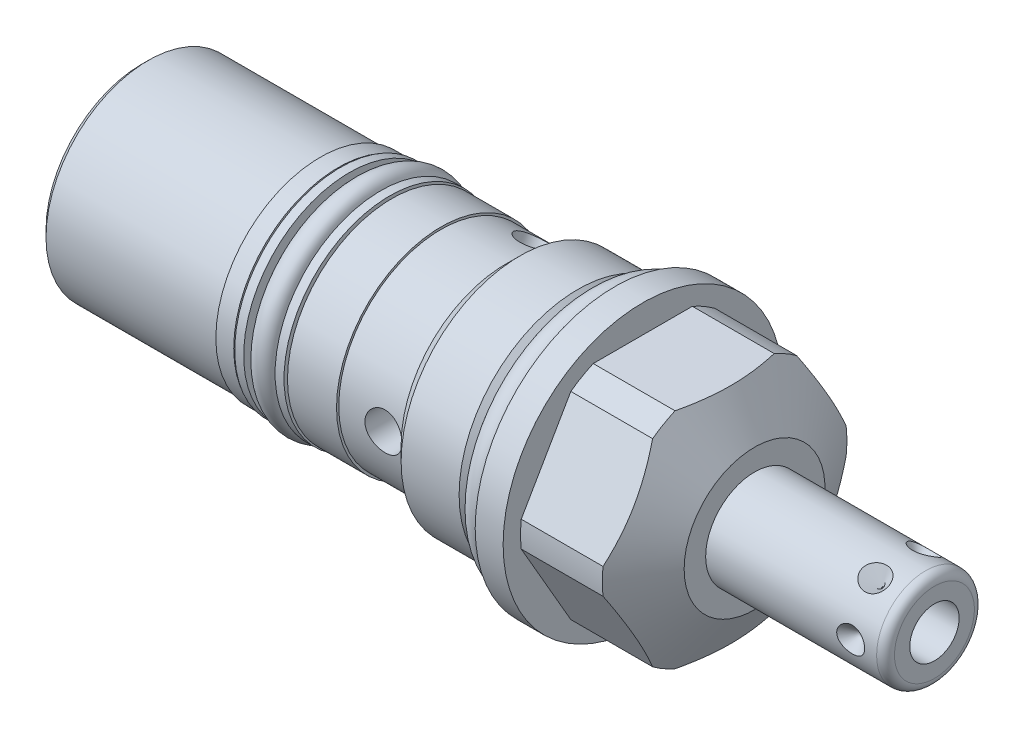
SolidWorks part; units mm, degrees
material "Alloy Steel"
ref_plane "Front Plane" through (0, 0, 0) normal (0, 0, 1) x (1, 0, 0)
ref_plane "Top Plane" through (0, 0, 0) normal (0, 1, 0) x (1, 0, 0)
ref_plane "Right Plane" through (0, 0, 0) normal (1, 0, 0) x (0, 0, -1)
sketch "Sketch1" plane through (0, 0, 0) normal (0, 0, 1) x (1, 0, 0)
  line L0 (0, 0) -> (113.8544, 0) construction
  line L1 (0, 15.875) -> (3.175, 15.875)
  line L2 (3.175, 15.875) -> (3.175, 13.8938)
  line L3 (3.175, 13.8938) -> (12.4728, 13.8938)
  line L4 (12.4728, 13.8938) -> (15.875, 8.001)
  line L5 (15.875, 8.001) -> (15.875, 0)
  line L6 (15.875, 0) -> (-53.7972, 0)
  line L7 (-53.7972, 0) -> (-53.7972, 11.6205)
  line L8 (0, 15.875) -> (0, 12.0015)
  line L9 (0, 12.0015) -> (-2.7178, 12.0015)
  line L10 (-2.7178, 12.0015) -> (-4.21, 13.4937)
  line L11 (-4.21, 13.4937) -> (-10.8013, 13.4937)
  line L12 (-10.8013, 13.4937) -> (-12.4206, 11.8745)
  line L14 (-12.4206, 11.8745) -> (-12.4206, 11.6205)
  line L15 (-12.4206, 11.6205) -> (-53.7972, 11.6205)
  dimension "D1" = 31.75
  dimension "D2" = 16.002
  dimension "D3" = 3.175
  dimension "D4" = 15.875
  dimension "D5" = 27.7876
  dimension "D6" = 30
  dimension "D7" = 53.7972
  dimension "D8" = 51.0794
  dimension "D9" = 24.003
  dimension "D10" = 45
  dimension "D11" = 26.9875
  dimension "D12" = 9.7028
  dimension "D13" = 23.749
  dimension "D14" = 23.241
revolve "Revolve1" add sketch "Sketch1" angle 360 about L0
sketch "Sketch2" plane through (15.875, 0, 0) normal (1, 0, 0) x (0, 0, -1)
  line L1 (7.3323, 12.7) -> (-7.3323, 12.7)
  line L2 (-7.3323, 12.7) -> (-14.6647, 0)
  line L3 (-14.6647, 0) -> (-7.3323, -12.7)
  line L4 (-7.3323, -12.7) -> (7.3323, -12.7)
  line L5 (7.3323, -12.7) -> (14.6647, 0)
  line L6 (14.6647, 0) -> (7.3323, 12.7)
  circle A0 centre (0, 0) radius 12.7 construction
  dimension "D1" = 25.4
extrude "Cut-Extrude1" cut sketch "Sketch2" against normal up to surface (12.7 mm away) flip side to cut up to face at (3.175, 0, 15.875)
sketch "Sketch3" plane through (0, 0, 0) normal (0, 0, 1) x (1, 0, 0)
  line L0 (0, 0) -> (52.5154, 0) construction
  line L1 (15.875, 5.5563) -> (35.306, 5.5562)
  line L2 (15.875, -8.001) -> (15.875, 8.001) construction
  line L3 (36.322, 4.5402) -> (36.322, 0)
  line L4 (36.322, 0) -> (15.875, 0)
  line L5 (15.875, 0) -> (15.875, 5.5563)
  line L6 (0, 15.875) -> (0, -15.875) construction
  arc A0 (36.322, 4.5402) -> (35.306, 5.5562) centre (35.306, 4.5402) ccw
  dimension "D1" = 1.016
  dimension "D2" = 36.322
  dimension "D3" = 11.1125
revolve "Revolve2" add sketch "Sketch3" angle 360 about L0
sketch "Sketch4" plane through (0, 0, 0) normal (0, 1, 0) x (1, 0, 0)
  line L0 (32.3596, 10.0738) -> (32.3596, 0) construction
  line L1 (36.322, -4.5402) -> (36.322, 4.5402) construction
  line L2 (33.9471, 5.5563) -> (32.3596, 5.5563)
  line L3 (35.306, 5.5563) -> (15.875, 5.5563) construction
  line L4 (32.3596, 5.5563) -> (32.3596, 3.9687)
  line L5 (32.3596, 3.9687) -> (33.9471, 5.5563)
  dimension "D1" = 3.9624
  dimension "D2" = 45
  dimension "D3" = 3.175
revolve "Cut-Revolve1" cut sketch "Sketch4" angle 360 about L0
pattern_circular "CirPattern1" count 6 over 360 about axis through (0, 0, 0) along (-1, 0, 0) of "Cut-Revolve1"
sketch "Sketch5" plane through (0, 0, 0) normal (0, 0, 1) x (1, 0, 0)
  line L0 (0, 0) -> (44.9273, 0) construction
  line L1 (36.322, 2.8067) -> (26.162, 2.8067)
  line L2 (36.322, -4.5402) -> (36.322, 4.5402) construction
  line L3 (26.162, 2.8067) -> (24.4756, 0)
  line L4 (24.4756, 0) -> (36.322, 0)
  line L5 (36.322, 0) -> (36.322, 2.8067)
  dimension "D1" = 10.16
  dimension "D2" = 59
  dimension "D3" = 5.6134
revolve "Cut-Revolve2" cut sketch "Sketch5" angle 360 about L0
sketch "Sketch6" plane through (0, 0, 0) normal (0, 0, 1) x (1, 0, 0)
  line L0 (-19.7612, 11.6205) -> (-19.7612, 11.8745)
  line L1 (-12.4206, 11.6205) -> (-53.7972, 11.6205) construction
  line L2 (-19.7612, 11.8745) -> (-33.4772, 11.8745)
  line L3 (-33.4772, 11.8745) -> (-33.4772, 11.6205)
  line L4 (-33.4772, 11.6205) -> (-19.7612, 11.6205)
  line L5 (0, 0) -> (-62.9111, 0) construction
  line L6 (-53.7972, 11.6205) -> (-53.7972, -11.6205) construction
  dimension "D1" = 13.716
  dimension "D2" = 23.749
  dimension "D3" = 20.32
revolve "Revolve3" add sketch "Sketch6" angle 360 about L5
sketch "Sketch7" plane through (-53.7972, 0, 0) normal (-1, 0, 0) x (0, 0, 1)
  circle A0 centre (0, 0) radius 0.8001
  dimension "D1" = 1.6002
extrude "Cut-Extrude2" cut sketch "Sketch7" against normal blind 0.762
sketch "Sketch8" plane through (0, 0, 0) normal (0, 0, 1) x (1, 0, 0)
  line L0 (0, 0) -> (-56.7277, 0) construction
  line L1 (-19.7612, 11.8745) -> (-33.4772, 11.8745) construction
  line L2 (-31.4452, 11.8745) -> (-25.3365, 11.8745)
  line L3 (-31.4452, 11.8745) -> (-31.4452, 9.8298)
  line L4 (-31.4452, 9.8298) -> (-25.3365, 9.8298)
  line L5 (-25.3365, 11.8745) -> (-25.3365, 9.8298)
  line L6 (-53.7972, 11.6205) -> (-53.7972, -11.6205) construction
  dimension "D1" = 6.1087
  dimension "D2" = 22.352
  dimension "D3" = 19.6596
revolve "Cut-Revolve3" cut sketch "Sketch8" angle 360 about L0
sketch "Sketch9" plane through (0, 0, 0) normal (0, 0, 1) x (1, 0, 0)
  line L0 (0, 0) -> (-59.2046, 0) construction
  line L1 (-28.3908, 14.9069) -> (-28.3908, -14.8344) construction
  line L2 (-31.4452, -11.8745) -> (-31.4452, 11.8745) construction
  line L3 (-25.3365, 9.8298) -> (-25.3365, -9.8298) construction
  line L4 (-25.3365, 9.8298) -> (-31.4452, 9.8298) construction
  line L5 (-26.6065, 12.0142) -> (-25.5905, 12.0142)
  line L6 (-26.6065, 12.0142) -> (-26.6065, 9.8298)
  line L7 (-26.6065, 9.8298) -> (-25.5905, 9.8298)
  line L8 (-25.5905, 12.0142) -> (-25.5905, 9.8298)
  line L9 (-25.3365, 11.8745) -> (-25.3365, -11.8745) construction
  line L10 (-31.1912, 12.0142) -> (-31.1912, 9.8298)
  line L11 (-30.1752, 9.8298) -> (-31.1912, 9.8298)
  line L12 (-30.1752, 12.0142) -> (-30.1752, 9.8298)
  line L13 (-30.1752, 12.0142) -> (-31.1912, 12.0142)
  dimension "D1" = 1.016
  dimension "D2" = 0.254
  dimension "D3" = 2.1844
revolve "Revolve4" add sketch "Sketch9" angle 360 about L0
sketch "Sketch10" plane through (0, 0, 0) normal (0, 1, 0) x (1, 0, 0)
  line L0 (-14.6812, 23.0369) -> (-14.6812, -3.4735) construction
  line L1 (-53.7972, 11.6205) -> (-53.7972, -11.6205) construction
  line L2 (-14.6812, -11.6205) -> (-16.7894, -11.6205)
  line L4 (-16.7894, -11.6205) -> (-16.7894, -0.7937)
  line L5 (-16.7894, -0.7937) -> (-14.6812, -0.7937)
  line L6 (-14.6812, -0.7937) -> (-14.6812, -11.6205)
  line L7 (-19.7612, -11.6205) -> (-12.4206, -11.6205) construction
  dimension "D1" = 39.116
  dimension "D2" = 4.2164
  dimension "D3" = 0.7937
revolve "Cut-Revolve4" cut sketch "Sketch10" angle 360 about L0
pattern_circular "CirPattern2" count 3 over 360 about axis through (0, 0, 0) along (1, 0, 0) of "Cut-Revolve4"
chamfer "Chamfer1" distance 0.762 angle 45 1 edges at (-53.7972, 0, 11.6205)
sketch "Sketch11" plane through (0, 0, 0) normal (0, 0, 1) x (1, 0, 0)
  line L0 (0, 0) -> (23.6366, 0) construction
  line L1 (0, 15.875) -> (0, -15.875) construction
  line L2 (0, 12.0015) -> (-2.7178, 12.0015) construction
  circle A0 centre (-1.4732, 13.4747) radius 1.4732
  dimension "D1" = 2.9464
  dimension "D2" = 26.9494
revolve "Revolve5" add sketch "Sketch11" angle 360 about L0
sketch "Sketch12" plane through (0, 0, 0) normal (0, 0, 1) x (1, 0, 0)
  line L0 (0, 0) -> (-56.0967, 0) construction
  line L1 (-26.6065, 9.8298) -> (-30.1752, 9.8298) construction
  line L2 (-28.3908, 11.1379) -> (-28.3908, 6.0377) construction
  line L3 (-31.4452, -11.8745) -> (-31.4452, 11.8745) construction
  line L4 (-25.3365, 9.8298) -> (-25.3365, -9.8298) construction
  circle A0 centre (-28.3908, 11.1379) radius 1.3081
  dimension "D1" = 2.6162
revolve "Revolve7" add sketch "Sketch12" angle 360 about L0
